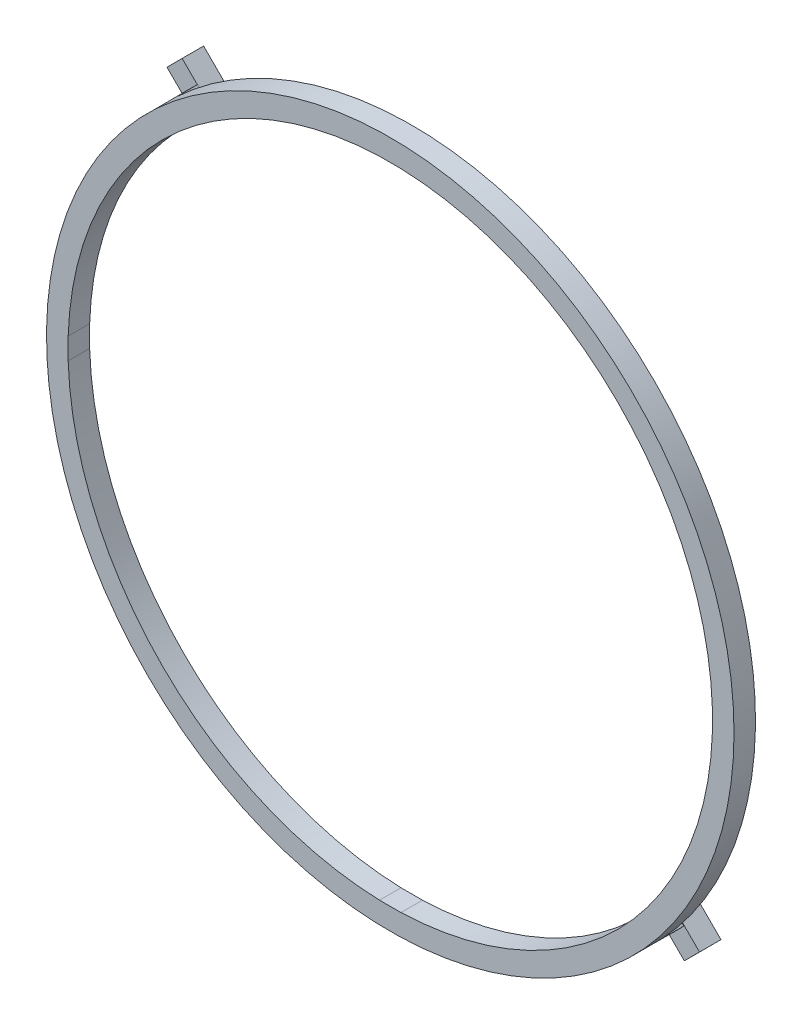
SolidWorks part; units mm, degrees
ref_plane "Front Plane" through (0, 0, 0) normal (0, 0, 1) x (1, 0, 0)
ref_plane "Top Plane" through (0, 0, 0) normal (0, 1, 0) x (1, 0, 0)
ref_plane "Right Plane" through (0, 0, 0) normal (1, 0, 0) x (0, 0, -1)
sketch "Sketch5" plane through (0, 0, 0) normal (0, 0, 1) x (1, 0, 0)
  line L0 (0, 15) -> (0, -15) construction
  line L1 (15, 0) -> (-15, 0) construction
  line L10 (13.9625, 13.9624) -> (-17.8573, -17.8574) construction
  line L11 (-12.766, 12.766) -> (14.8988, -14.8988) construction
  line L12 (-0.5, -14.9917) -> (0.5, -14.9917)
  line L13 (14.9917, -0.5) -> (14.9917, 0.5)
  line L14 (-0.5, 14.9917) -> (0.5, 14.9917)
  line L15 (-14.9917, -0.5) -> (-14.9917, 0.5)
  arc A0 (-14.9917, -0.5) -> (-0.5, -14.9917) centre (0, 0) ccw
  circle A1 centre (0, 0) radius 16
  arc A2 (14.9917, 0.5) -> (0.5, 14.9917) centre (0, 0) ccw
  arc A3 (-0.5, 14.9917) -> (-14.9917, 0.5) centre (0, 0) ccw
  arc A4 (0.5, -14.9917) -> (14.9917, -0.5) centre (0, 0) ccw
  dimension "D1" = 30
  dimension "D2" = 1
extrude "Boss-Extrude1" add sketch "Sketch5" along normal blind 1
sketch "Sketch6" plane through (0, 0, 0) normal (0, 0, 1) x (1, 0, 0)
  line L0 (-11.6618, 10.9546) -> (-10.9757, 10.2242)
  line L2 (-10.9547, 11.6617) -> (-10.27, 10.9328)
  line L4 (0, 0) -> (-12.313, 12.313) construction
  arc A2 (-10.9547, 11.6617) -> (-11.6618, 10.9546) centre (0, 0) ccw
  arc A4 (-10.27, 10.9328) -> (-10.9757, 10.2242) centre (0, 0) ccw
extrude "Boss-Extrude7" add sketch "Sketch6" against normal blind 1
sketch "Sketch8" plane through (0, 0, -1) normal (0, 0, -1) x (-1, 0, 0)
  line L0 (10.9757, 10.2242) -> (10.27, 10.9328)
  line L1 (10.9757, 10.2242) -> (12.3928, 11.6355)
  line L2 (10.27, 10.9328) -> (11.6872, 12.3441)
  line L3 (12.3928, 11.6355) -> (11.6872, 12.3441)
  dimension "D1" = 2
extrude "Boss-Extrude8" add sketch "Sketch8" along normal blind 1
pattern_circular "CirPattern1" count 2 over 360 about axis through (0, 0, 0) along (0, 0, 1) of "Boss-Extrude7", "Boss-Extrude8"
